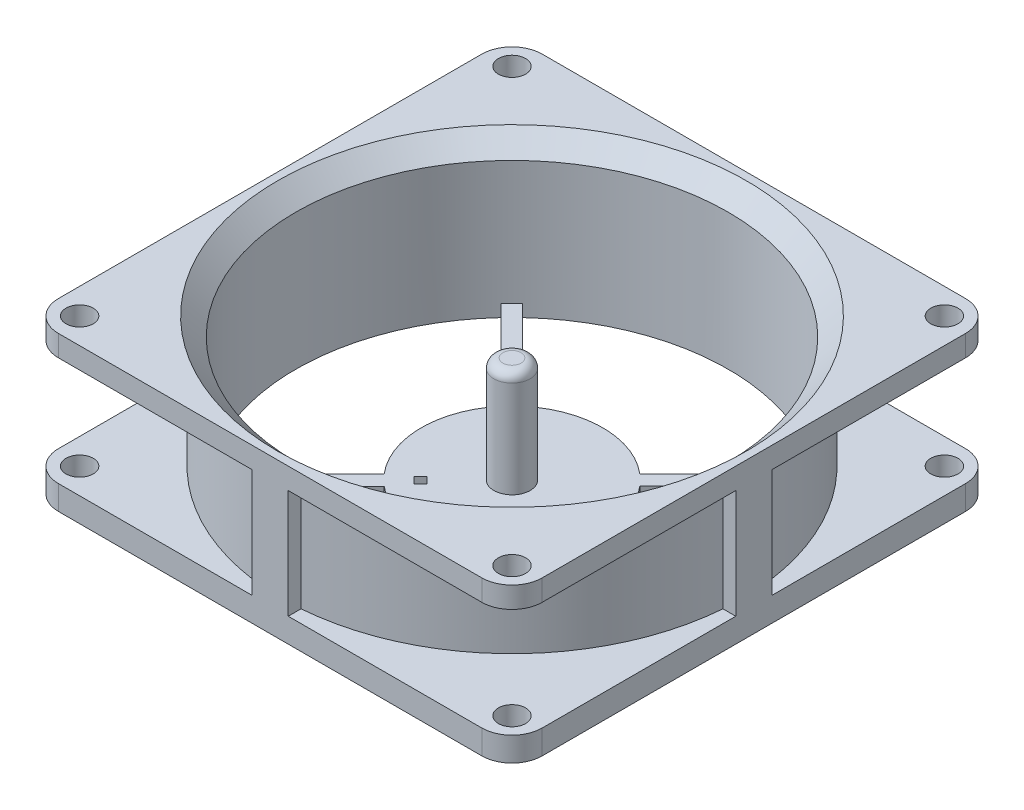
SolidWorks part; units mm, degrees
ref_plane "Front Plane" through (0, 0, 0) normal (0, 0, 1) x (1, 0, 0)
ref_plane "Top Plane" through (0, 0, 0) normal (0, 1, 0) x (1, 0, 0)
ref_plane "Right Plane" through (0, 0, 0) normal (1, 0, 0) x (0, 0, -1)
sketch "Sketch1" plane through (0, 0, 0) normal (0, 1, 0) x (1, 0, 0)
  line L1 (-40, 40) -> (40, 40)
  line L2 (-40, 40) -> (-40, -40)
  line L3 (-40, -40) -> (40, -40)
  line L4 (40, 40) -> (40, -40)
  dimension "D1" = 80
  dimension "D2" = 80
  dimension "D3" = 40
  dimension "D4" = 40
extrude "Boss-Extrude1" add sketch "Sketch1" along normal blind 25.5
sketch "Sketch2" plane through (0, 25.5, 0) normal (0, 1, 0) x (1, 0, 0)
  circle A0 centre (0, 0) radius 35.75
  dimension "D1" = 71.5
extrude "Cut-Extrude2" cut sketch "Sketch2" against normal blind 28
sketch "Sketch4" plane through (0, 0, 0) normal (0, -1, 0) x (1, 0, 0)
  line L0 (0, 0) -> (0, 35.75) construction
  line L1 (0, 0) -> (-35.75, 0) construction
  line L2 (-1.75, 0) -> (0, 1.7855)
  line L3 (-24.3705, 26.1561) -> (0, 1.7855)
  line L4 (-26.1389, 24.3889) -> (-1.75, 0)
  circle A0 centre (0, 0) radius 35.75 construction
  arc A1 (-24.3705, 26.1561) -> (-26.1389, 24.3889) centre (0, 0) ccw
  dimension "D1" = 2.5
  dimension "D2" = 1.75
  dimension "D3" = 45
extrude "Boss-Extrude2" add sketch "Sketch4" against normal blind 2
pattern_circular "CirPattern2" count 4 every 90 about axis through (0, 0, 0) along (0, 1, 0) of "Boss-Extrude2"
sketch "Sketch5" plane through (0, 0, 0) normal (0, -1, 0) x (1, 0, 0)
  circle A0 centre (0, 0) radius 15
  dimension "D1" = 30
extrude "Boss-Extrude3" add sketch "Sketch5" against normal blind 2
sketch "Sketch6" plane through (0, 2, 0) normal (0, 1, 0) x (1, 0, 0)
  circle A0 centre (0, 0) radius 3
extrude "Boss-Extrude4" add sketch "Sketch6" along normal blind 17.5
fillet "Fillet1" radius 1.5 1 edges at (0, 19.5, 3)
ref_plane "Plane1" through (0, 4, 0) normal (0, -1, 0) x (1, 0, 0)
sketch "Sketch7" plane through (0, 4, 0) normal (0, -1, 0) x (1, 0, 0)
  circle A0 centre (0, 0) radius 38
  circle A1 centre (0, 0) radius 70
  dimension "D1" = 76
extrude "Cut-Extrude4" cut sketch "Sketch7" against normal blind 18
fillet "Fillet2" radius 5 8 edges at (40, 2, -40) (40, 23.75, -40) (-40, 23.75, -40) (-40, 2, -40) (-40, 2, 40) (-40, 23.75, 40) (40, 23.75, 40) (40, 2, 40)
sketch "Sketch8" plane through (0, 4, 0) normal (0, -1, 0) x (1, 0, 0)
  line L0 (35, 40) -> (-35, 40) construction
  line L1 (-3, 40) -> (3, 40)
  line L2 (-3, 40) -> (-3, 35.6239)
  line L4 (3, 40) -> (3, 35.6239)
  circle A0 centre (0, 0) radius 35.75 construction
  arc A1 (-3, 35.6239) -> (3, 35.6239) centre (0, 0) cw
  dimension "D1" = 3
  dimension "D2" = 3
extrude "Boss-Extrude5" add sketch "Sketch8" against normal blind 20
pattern_circular "CirPattern3" count 4 every 90 about axis through (0, 0, 0) along (0, 1, 0) of "Boss-Extrude5"
sketch "Sketch9" plane through (0, 25.5, 0) normal (0, 1, 0) x (-1, 0, 0)
  circle A0 centre (35.75, -35.75) radius 2.25
  dimension "D3" = 4.5
  dimension "D1" = 35.75
  dimension "D2" = 35.75
extrude "Cut-Extrude5" cut sketch "Sketch9" against normal blind 37
pattern_linear "LPattern1" count 2 spacing 71.5 along (1, 0, 0) count 2 spacing 71.5 along (0, 0, 1) of "Cut-Extrude5"
chamfer "Chamfer2" distance 3 angle 45 1 edges at (0, 25.5, 35.75)
sketch "Sketch11" plane through (0, 0, 0) normal (0, -1, 0) x (1, 0, 0)
  line L0 (-28.8632, 27.8203) -> (-7.5549, 6.512)
  line L1 (-7.5549, 6.512) -> (-6.4942, 7.5726)
  line L2 (-6.4942, 7.5726) -> (-28.2419, 29.3203)
  line L3 (-28.8632, 27.8203) -> (-40, 27.8203)
  line L4 (-9.6762, 11.4617) -> (-24.3705, 26.1561) construction
  line L5 (-26.1389, 24.3889) -> (-11.4454, 9.6954) construction
  line L6 (-40, -35) -> (-40, 35) construction
  line L7 (-40, 27.8203) -> (-40, 29.3203)
  line L8 (-40, 29.3203) -> (-28.2419, 29.3203)
  dimension "D1" = 0.5
  dimension "D2" = 0.5
  dimension "D3" = 5
  dimension "D4" = 5
  dimension "D5" = 1.5
extrude "Cut-Extrude6" cut sketch "Sketch11" against normal blind 1
sketch "Sketch12" plane through (0, 1, 0) normal (0, -1, 0) x (1, 0, 0)
  line L0 (-6.4942, 7.5726) -> (-7.5549, 8.6333)
  line L1 (-6.4942, 7.5726) -> (-28.2419, 29.3203) construction
  line L2 (-7.5549, 8.6333) -> (-8.6155, 7.5726)
  line L3 (-28.8632, 27.8203) -> (-7.5549, 6.512) construction
  line L4 (-8.6155, 7.5726) -> (-7.5549, 6.512)
  line L5 (-7.5549, 6.512) -> (-6.4942, 7.5726)
  dimension "D1" = 1.5
extrude "Cut-Extrude7" cut sketch "Sketch12" against normal blind 7
